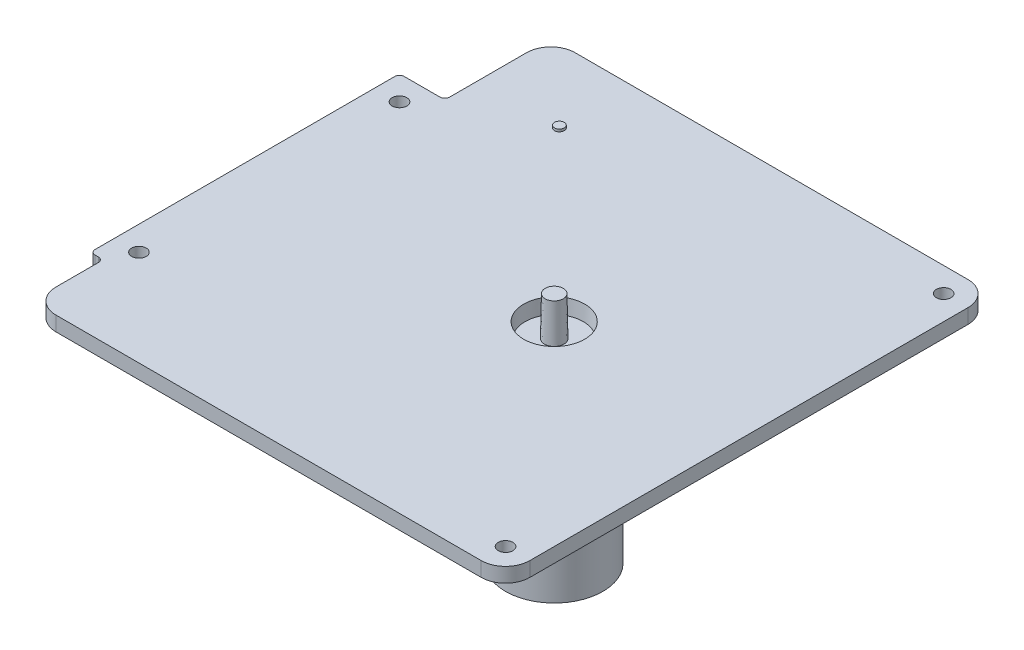
SolidWorks part; units mm, degrees
ref_plane "Front Plane" through (0, 0, 0) normal (0, 0, 1) x (1, 0, 0)
ref_plane "Top Plane" through (0, 0, 0) normal (0, 1, 0) x (1, 0, 0)
ref_plane "Right Plane" through (0, 0, 0) normal (1, 0, 0) x (0, 0, -1)
ref_plane "Plane1" through (0, 23, 0) normal (0, 1, 0) x (1, 0, 0)
sketch "Sketch1" plane through (0, 23, 0) normal (0, 1, 0) x (1, 0, 0)
  line L0 (98.3054, 50) -> (98.3054, 28.2195)
  line L1 (189, 50) -> (98.3054, 50)
  line L2 (189, 50) -> (189, -50)
  line L3 (189, -50) -> (97.6502, -50)
  line L5 (98.3054, 28.2195) -> (89, 28.2195)
  line L6 (89, 28.2195) -> (89, -35.308)
  line L7 (89, -35.308) -> (91.6598, -35.308)
  line L8 (91.6598, -35.308) -> (91.6598, -50)
  line L9 (91.6598, -50) -> (97.6502, -50)
  line L10 (94.8054, 33.2195) -> (98.3054, 33.2195) construction
  line L11 (184, 45) -> (184, 50) construction
  line L12 (93.3054, 31.7195) -> (93.3054, 28.2195) construction
  line L13 (99.4745, -35.308) -> (86.1225, -35.308) construction
  line L14 (88.1598, -40.308) -> (91.6598, -40.308) construction
  line L15 (86.6598, -38.808) -> (86.6598, -35.308) construction
  line L16 (189, 0) -> (190, 0) construction
  line L17 (190, -60) -> (190, 60) construction
  line L18 (105.0183, -40) -> (185.0183, -40) construction
  line L19 (105.0183, -40) -> (105.0183, 40) construction
  line L20 (105.0183, 40) -> (185.0183, 40) construction
  line L21 (185.0183, -40) -> (185.0183, 40) construction
  line L22 (184, 45) -> (189, 45) construction
  line L23 (184, -45) -> (189, -45) construction
  line L24 (184, -45) -> (184, -50) construction
  line L25 (94, 23.2195) -> (94, 28.2195) construction
  line L26 (94, 23.2195) -> (89, 23.2195) construction
  line L27 (94, -30.308) -> (94, -35.308) construction
  line L28 (94, -30.308) -> (89, -30.308) construction
  line L29 (190, -55) -> (190, 55) construction
  circle A0 centre (86.6598, -40.308) radius 1.5 construction
  circle A1 centre (93.3054, 33.2195) radius 1.5 construction
  circle A2 centre (184, 45) radius 1.5 construction
  circle A3 centre (184, 45) radius 1.5 construction
  circle A4 centre (184, -45) radius 1.5 construction
  circle A6 centre (94, 23.2195) radius 1.5 construction
  circle A7 centre (94, -30.308) radius 1.5 construction
  point P32 (185.0183, 0)
  dimension "D1" = 100
  dimension "D2" = 80
  dimension "D3" = 3.5
  dimension "D4" = 5
  dimension "D5" = 1
  dimension "D6" = 100
extrude "Boss-Extrude1" add sketch "Sketch1" along normal blind 3
fillet "Fillet3" radius 5 4 edges at (189, 24.5, -50) (98.3054, 24.5, -50) (91.6598, 24.5, 50) (189, 24.5, 50)
fillet "Fillet2" radius 1 4 edges at (89, 24.5, -28.2195) (98.3054, 24.5, -28.2195) (91.6598, 24.5, 35.308) (89, 24.5, 35.308)
sketch "Sketch2" plane through (0, 23, 0) normal (0, 1, 0) x (1, 0, 0)
  circle A0 centre (184, -45) radius 1.5 construction
  circle A1 centre (184, -45) radius 1.5
  circle A2 centre (94, -30.308) radius 1.5 construction
  circle A3 centre (94, -30.308) radius 1.5
  circle A4 centre (94, 23.2195) radius 1.5 construction
  circle A5 centre (94, 23.2195) radius 1.5
  circle A6 centre (184, 45) radius 1.5 construction
  circle A7 centre (184, 45) radius 1.5
extrude "Cut-Extrude1" cut sketch "Sketch2" along normal up to surface (3 mm away) up to face at (116.9913, 26, 1.7721)
sketch "Sketch5" plane through (0, 23, 0) normal (0, 1, 0) x (1, 0, 0)
  line L0 (189, 50) -> (189, -50) construction
  circle A0 centre (149, 0) radius 10
  circle A1 centre (149, 0) radius 6 construction
  circle A2 centre (149, 0) radius 2 construction
  circle A3 centre (149, 0) radius 33.75 construction
  circle A4 centre (115.0653, 35) radius 15 construction
  point P4 (189, 0)
  dimension "D2" = 20
  dimension "D3" = 12
  dimension "D4" = 4
  dimension "D5" = 67.5
  dimension "D6" = 30
  dimension "D1" = 40
  dimension "D7" = 35
extrude "Boss-Extrude2" add sketch "Sketch5" against normal blind 40
sketch "Sketch3" plane through (0, 23, 0) normal (0, 1, 0) x (1, 0, 0)
  line L0 (189, 50) -> (189, -50) construction
  circle A0 centre (149, 0) radius 6
  circle A1 centre (149, 0) radius 6 construction
  point P6 (189, 0)
extrude "Cut-Extrude3" cut sketch "Sketch3" along normal blind 3 draft 5 draft outward yes
sketch "Sketch6" plane through (0, 23, 0) normal (0, 1, 0) x (1, 0, 0)
  circle A0 centre (149, 0) radius 2
  circle A1 centre (149, 0) radius 2 construction
extrude "Boss-Extrude3" add sketch "Sketch6" along normal blind 8 draft 1
sketch "Sketch7" plane through (0, 26, 0) normal (0, 1, 0) x (1, 0, 0)
  circle A0 centre (115.0653, 35) radius 1
  dimension "D1" = 2
extrude "Boss-Extrude4" add sketch "Sketch7" along normal blind 0.5
sketch "Sketch8" plane through (0, 26, 0) normal (0, 1, 0) x (1, 0, 0)
  line L0 (105.9564, 52.0218) -> (123.7032, 51.8404)
  line L1 (105.9564, 24.4078) -> (123.7032, 24.4078)
  line L2 (105.9564, 24.4078) -> (105.9564, 56.7922)
  line L3 (105.9564, 56.7922) -> (123.7032, 56.7922)
  line L4 (123.7032, 24.4078) -> (123.7032, 56.7922)
  line L5 (105.9564, 27.6322) -> (123.7032, 28.0197)
